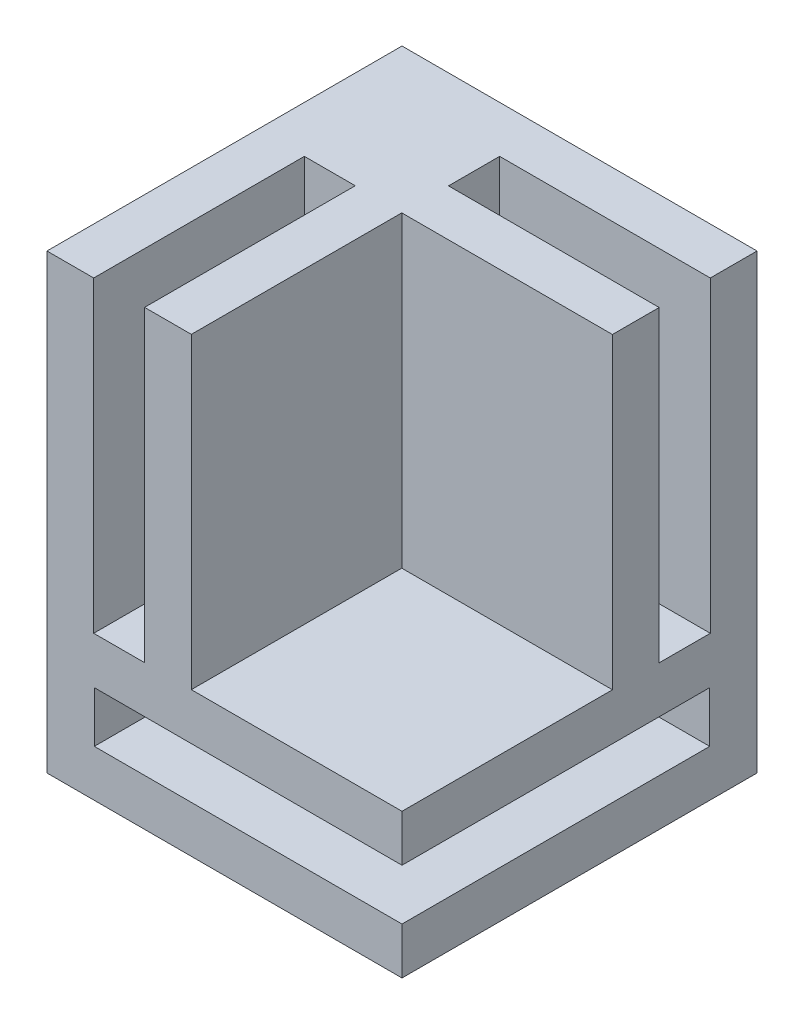
SolidWorks part; units mm, degrees
ref_plane "Plan de face" through (0, 0, 0) normal (0, 0, 1) x (1, 0, 0)
ref_plane "Plan de dessus" through (0, 0, 0) normal (0, 1, 0) x (1, 0, 0)
ref_plane "Plan de droite" through (0, 0, 0) normal (1, 0, 0) x (0, 0, -1)
sketch "Sketch1" plane through (0, 0, 0) normal (0, 0, 1) x (1, 0, 0)
  line L1 (-41.2499, 24.2978) -> (-11.2499, 24.2978)
  line L2 (-41.2499, 24.2978) -> (-41.2499, 12.0978)
  line L3 (-41.2499, 12.0978) -> (-11.2499, 12.0978)
  line L4 (-11.2499, 24.2978) -> (-11.2499, 12.0978)
  dimension "D1" = 12.2
  dimension "D2" = 30
extrude "Boss-Extrude1" add sketch "Sketch1" along normal blind 30
sketch "Sketch2" plane through (-11.2499, 0, 0) normal (1, 0, 0) x (0, 0, -1)
  line L0 (-30, 12.0978) -> (-30, 24.2978) construction
  line L1 (-30, 20.3478) -> (-4, 20.3478)
  line L2 (-30, 20.3478) -> (-30, 16.0478)
  line L3 (-30, 16.0478) -> (-4, 16.0478)
  line L4 (-4, 20.3478) -> (-4, 16.0478)
  line L5 (-30, 24.2978) -> (0, 24.2978) construction
  line L6 (-30, 12.0978) -> (0, 12.0978) construction
  line L7 (0, 12.0978) -> (0, 24.2978) construction
  dimension "D1" = 3.95
  dimension "D2" = 3.95
  dimension "D3" = 4.3
  dimension "D4" = 4
extrude "Cut-Extrude1" cut sketch "Sketch2" against normal blind 26
sketch "Sketch3" plane through (0, 24.2978, 0) normal (0, 1, 0) x (1, 0, 0)
  line L5 (-41.2499, 0) -> (-11.2499, 0)
  line L6 (-41.2499, 0) -> (-41.2499, -30)
  line L7 (-41.2499, -30) -> (-11.2499, -30)
  line L8 (-11.2499, 0) -> (-11.2499, -30)
  dimension "D1" = 30
  dimension "D2" = 30
extrude "Boss-Extrude2" add sketch "Sketch3" along normal blind 26
sketch "Sketch4" plane through (0, 50.2978, 0) normal (0, 1, 0) x (1, 0, 0)
  line L1 (-11.2499, -30) -> (-29.0499, -30)
  line L2 (-11.2499, -30) -> (-11.2499, -12.22)
  line L3 (-11.2499, -12.22) -> (-29.0499, -12.22)
  line L4 (-29.0499, -30) -> (-29.0499, -12.22)
  line L6 (-11.2499, 0) -> (-41.2499, 0) construction
  line L7 (-41.2499, 0) -> (-41.2499, -30) construction
  dimension "D1" = 12.2
  dimension "D2" = 12.22
extrude "Cut-Extrude2" cut sketch "Sketch4" against normal blind 26
sketch "Sketch6" plane through (-11.2499, 0, 0) normal (1, 0, 0) x (0, 0, -1)
  line L0 (-12.22, 50.2978) -> (0, 50.2978) construction
  line L1 (-8.27, 50.2978) -> (-3.95, 50.2978)
  line L2 (-8.27, 50.2978) -> (-8.27, 24.2978)
  line L3 (-8.27, 24.2978) -> (-3.95, 24.2978)
  line L4 (-3.95, 50.2978) -> (-3.95, 24.2978)
  line L5 (0, 12.0978) -> (0, 50.2978) construction
  line L6 (-12.22, 24.2978) -> (-12.22, 50.2978) construction
  dimension "D1" = 26
  dimension "D2" = 3.95
  dimension "D3" = 3.95
extrude "Cut-Extrude3" cut sketch "Sketch6" against normal blind 17.8
sketch "Sketch9" plane through (0, 0, 30) normal (0, 0, 1) x (1, 0, 0)
  line L0 (-41.2499, 50.2978) -> (-29.0499, 50.2978) construction
  line L1 (-37.2999, 50.2978) -> (-32.9999, 50.2978)
  line L2 (-37.2999, 50.2978) -> (-37.2999, 24.2978)
  line L3 (-37.2999, 24.2978) -> (-32.9999, 24.2978)
  line L4 (-32.9999, 50.2978) -> (-32.9999, 24.2978)
  line L5 (-41.2499, 50.2978) -> (-41.2499, 12.0978) construction
  line L6 (-29.0499, 24.2978) -> (-29.0499, 50.2978) construction
  dimension "D1" = 26
  dimension "D2" = 3.95
  dimension "D3" = 3.95
extrude "Cut-Extrude4" cut sketch "Sketch9" against normal blind 17.8
